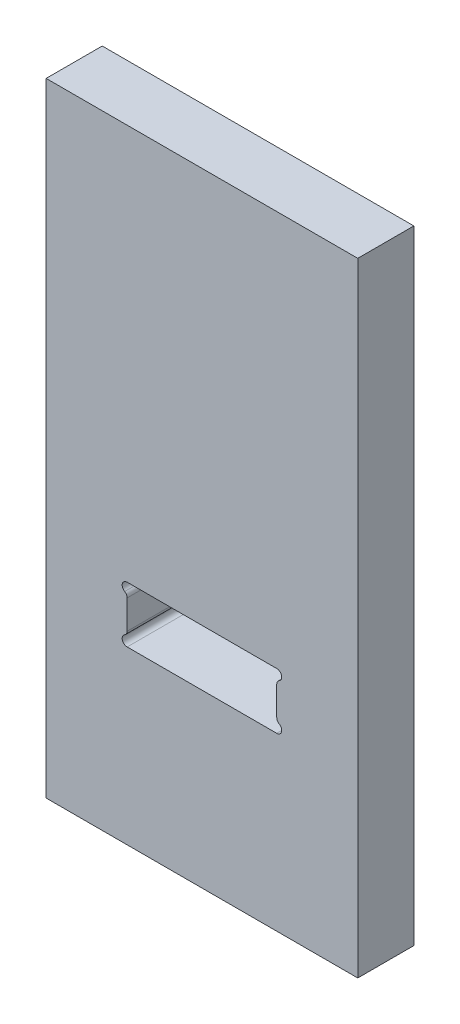
SolidWorks part; units mm, degrees
ref_plane "Front Plane" through (0, 0, 0) normal (0, 0, 1) x (1, 0, 0)
ref_plane "Top Plane" through (0, 0, 0) normal (0, 1, 0) x (1, 0, 0)
ref_plane "Right Plane" through (0, 0, 0) normal (1, 0, 0) x (0, 0, -1)
sketch "Sketch1" plane through (0, 0, 0) normal (0, 0, 1) x (1, 0, 0)
  line L1 (0, 0) -> (25, 0)
  line L2 (0, 0) -> (0, 50)
  line L3 (0, 50) -> (25, 50)
  line L4 (25, 0) -> (25, 50)
  dimension "D1" = 50
  dimension "D2" = 25
extrude "Boss-Extrude1" add sketch "Sketch1" along normal blind 4.5
sketch "Sketch3" plane through (0, 0, 4.5) normal (0, 0, 1) x (1, 0, 0)
  line L0 (12.5, 50) -> (12.5, 0) construction
  line L1 (25, 50) -> (0, 50) construction
  line L2 (0, 0) -> (25, 0) construction
  line L3 (6.5, 18.25) -> (18.5, 18.25)
  line L4 (18.5, 17.1572) -> (18.5, 14.8428)
  line L5 (18.5, 16) -> (12.5, 16) construction
  line L6 (6.5, 13.75) -> (18.5, 13.75)
  line L7 (6.5, 17.1572) -> (6.5, 14.8428)
  arc A0 (18.5, 18.25) -> (18.7, 17.5036) centre (18.5, 17.85) cw
  arc A1 (18.7, 17.5036) -> (18.5, 17.1572) centre (18.9, 17.1572) ccw
  arc A2 (18.7, 14.4964) -> (18.5, 14.8428) centre (18.9, 14.8428) cw
  arc A3 (18.5, 13.75) -> (18.7, 14.4964) centre (18.5, 14.15) ccw
  arc A4 (6.5, 13.75) -> (6.3, 14.4964) centre (6.5, 14.15) cw
  arc A5 (6.3, 14.4964) -> (6.5, 14.8428) centre (6.1, 14.8428) ccw
  arc A6 (6.3, 17.5036) -> (6.5, 17.1572) centre (6.1, 17.1572) cw
  arc A7 (6.5, 18.25) -> (6.3, 17.5036) centre (6.5, 17.85) ccw
  point P19 (12.5, 18.25)
  point P30 (12.5, 13.75)
  dimension "D1" = 0.4
  dimension "D2" = 4.5
  dimension "D3" = 12
  dimension "D4" = 16
extrude "Cut-Extrude2" cut sketch "Sketch3" against normal up to next
